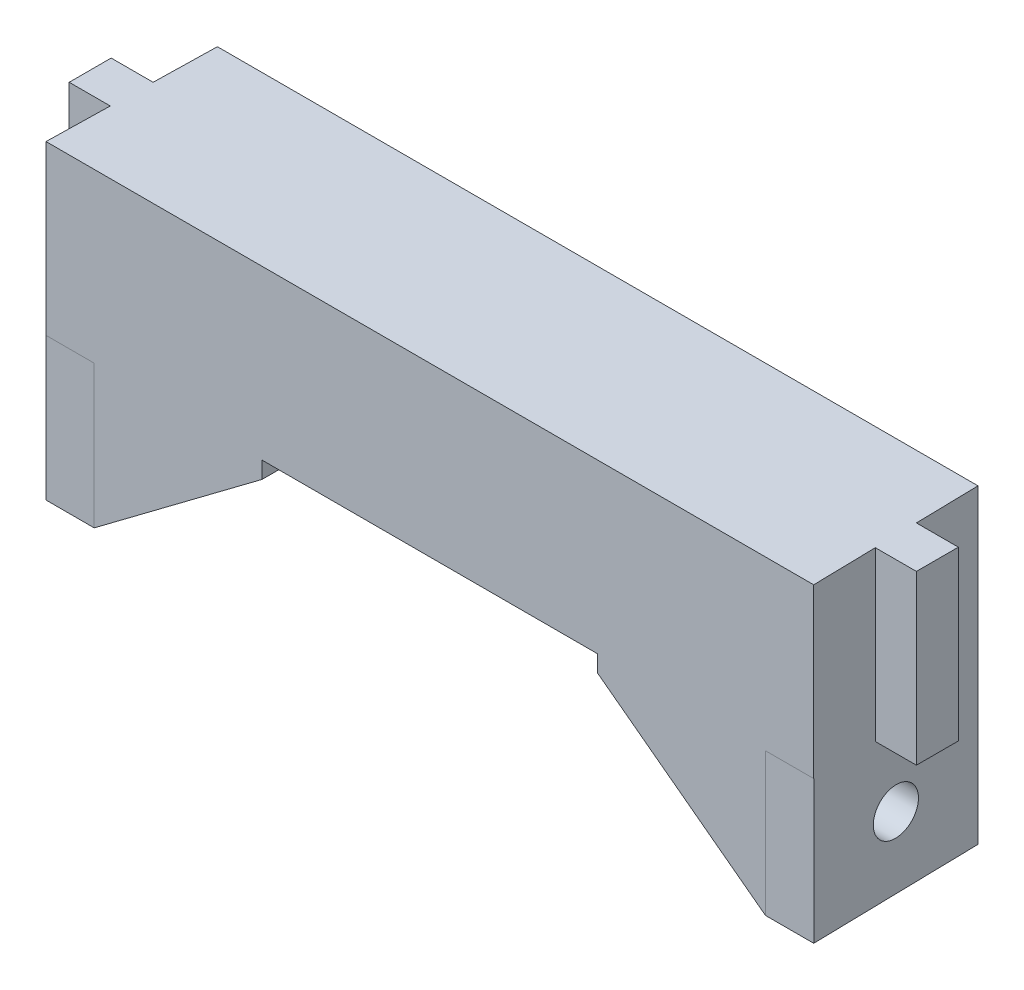
SolidWorks part; units mm, degrees
ref_plane "Front Plane" through (0, 0, 0) normal (0, 0, 1) x (1, 0, 0)
ref_plane "Top Plane" through (0, 0, 0) normal (0, 1, 0) x (1, 0, 0)
ref_plane "Right Plane" through (0, 0, 0) normal (1, 0, 0) x (0, 0, -1)
sketch "Sketch1" plane through (0, 0, 0) normal (0, 1, 0) x (1, 0, 0)
  line L0 (-45.74, 0) -> (-45.3158, 20)
  line L1 (-45.3158, 20) -> (45.3158, 20)
  line L2 (45.3158, 20) -> (45.74, 0)
  line L3 (45.74, 0) -> (-45.74, 0)
  point P4 (0, 0)
  point P7 (0, 20)
  dimension "D1" = 20
  dimension "D2" = 91.48
  dimension "D3" = 2.43
extrude "Boss-Extrude1" add sketch "Sketch1" along normal blind 20
sketch "Sketch2" plane through (0, 20, 0) normal (0, 1, 0) x (1, 0, 0)
  line L0 (45.74, 0) -> (45.3158, 20) construction
  line L1 (45.4749, 12.5) -> (50.4749, 12.5)
  line L2 (45.4749, 12.5) -> (45.4749, 7.5)
  line L3 (45.4749, 7.5) -> (50.4749, 7.5)
  line L4 (50.4749, 12.5) -> (50.4749, 7.5)
  line L5 (40.3158, 20) -> (40.3158, 0) construction
  line L6 (45.3158, 20) -> (-45.3158, 20) construction
  line L7 (-45.74, 0) -> (45.74, 0) construction
  line L8 (40.3158, 10) -> (45.5279, 10) construction
  line L9 (0, 0) -> (0, 20) construction
  line L10 (-45.4749, 7.5) -> (-50.4749, 7.5)
  line L11 (-50.4749, 12.5) -> (-50.4749, 7.5)
  line L12 (-45.4749, 12.5) -> (-50.4749, 12.5)
  line L13 (-45.4749, 12.5) -> (-45.4749, 7.5)
  point P14 (45.4749, 10)
  dimension "D1" = 5
  dimension "D2" = 5
  dimension "D3" = 5
extrude "Boss-Extrude2" add sketch "Sketch2" against normal up to surface (20 mm away) up to face at (0, 0, -10)
sketch "Sketch3" plane through (-45.7194, 0, -0.9697) normal (-0.9998, 0, -0.0212) x (-0.0212, 0, 0.9998)
  line L0 (0.9649, 0) -> (0.9649, -27.94) construction
  line L1 (-19.0346, 0) -> (0.9649, 0)
  line L2 (-19.0346, 0) -> (-19.0346, -17)
  line L3 (-19.0346, -17) -> (0.9649, -17)
  line L4 (0.9649, 0) -> (0.9649, -17)
  circle A0 centre (-9.0348, -8.5) radius 2.75 construction
  circle A1 centre (-9.0348, -8.5) radius 6.5 construction
  point P10 (-19.0346, -8.5)
  point P11 (-9.0348, 0)
  dimension "D2" = 5.5
  dimension "D3" = 13
  dimension "D1" = 17
ref_plane "Plane1" through (-40, 0, 0) normal (1, 0, 0) x (0, 0, -1)
sketch "Sketch4" plane through (-40, 0, 0) normal (1, 0, 0) x (0, 0, -1)
  line L4 (20, 0) -> (20, -17)
  line L5 (20, -17) -> (0, -17)
  line L6 (0, -17) -> (0, 0)
  line L7 (0, 0) -> (20, 0)
  line L11 (20, -17) -> (0.0049, -17) construction
loft "Loft1" add section "Sketch4" section "Sketch3"
ref_plane "Plane2" through (-20, 0, 0) normal (1, 0, 0) x (0, 0, -1)
sketch "Sketch5" plane through (-20, 0, 0) normal (1, 0, 0) x (0, 0, -1)
  line L1 (20, 0) -> (0, 0)
  line L2 (20, 0) -> (20, -2)
  line L3 (20, -2) -> (0, -2)
  line L4 (0, 0) -> (0, -2)
  dimension "D1" = 2
sketch "Sketch6" plane through (-40, 0, 0) normal (1, 0, 0) x (0, 0, -1)
  line L4 (20, 0) -> (0, 0)
  line L5 (0, 0) -> (0, -17)
  line L6 (0, -17) -> (20, -17)
  line L7 (20, -17) -> (20, 0)
  line L8 (20, 0) -> (0, 0)
  line L9 (0, 0) -> (0, -17)
  line L10 (0, -17) -> (20, -17)
  line L11 (20, -17) -> (20, 0)
  dimension "D1" = 0
loft "Loft3" add profiles "Sketch6", "Sketch5"
sketch "Sketch7" plane through (-40, 0, 0) normal (1, 0, 0) x (0, 0, -1)
  line L0 (0, 0) -> (20, 0) construction
  line L1 (20, 0) -> (20, -17) construction
  line L2 (10, 0) -> (10, -8.5) construction
  line L3 (10, -8.5) -> (20, -8.5) construction
  circle A0 centre (10, -8.5) radius 2.75
  dimension "D1" = 5.5
extrude "Cut-Extrude1" cut sketch "Sketch7" against normal through all
sketch "Sketch8" plane through (-40, 0, 0) normal (1, 0, 0) x (0, 0, -1)
  circle A0 centre (10, -8.5) radius 6.5
  circle A1 centre (10, -8.5) radius 2.75 construction
  dimension "D1" = 13
extrude "Cut-Extrude2" cut sketch "Sketch8" along normal blind 30
mirror "Mirror1" about plane through (0, 0, 0) normal (1, 0, 0) of "Cut-Extrude2", "Cut-Extrude1", "Loft3", "Loft1"
